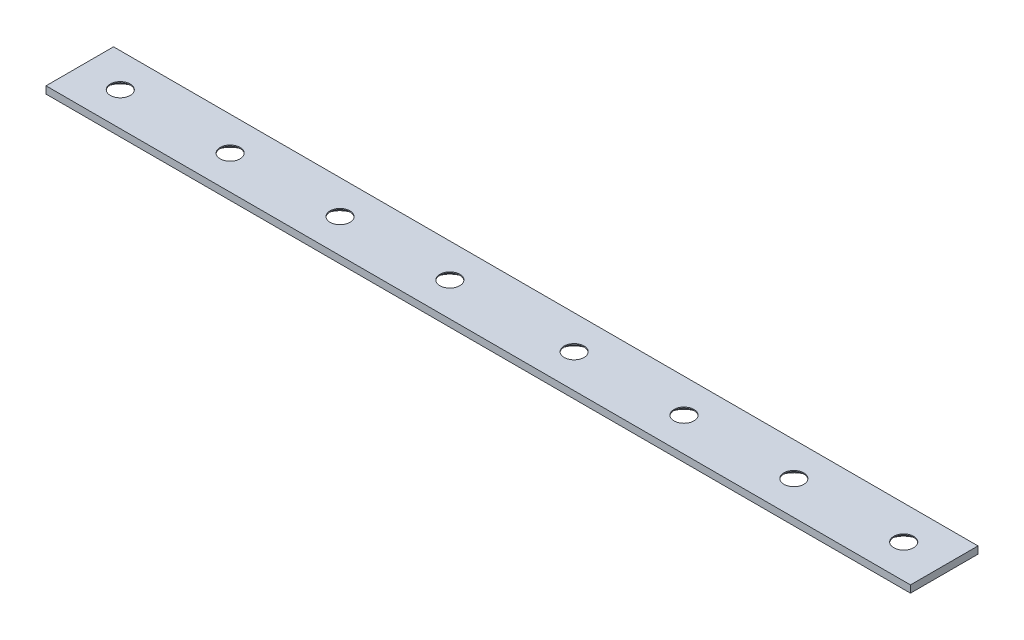
SolidWorks part; units mm, degrees
material "AISI 304"
ref_plane "Front Plane" through (0, 0, 0) normal (0, 0, 1) x (1, 0, 0)
ref_plane "Top Plane" through (0, 0, 0) normal (0, 1, 0) x (1, 0, 0)
ref_plane "Right Plane" through (0, 0, 0) normal (1, 0, 0) x (0, 0, -1)
sketch "Sketch1" plane through (0, 0, 0) normal (0, 1, 0) x (1, 0, 0)
  line L1 (0, 0) -> (243.84, 0)
  line L2 (0, 0) -> (0, 19.05)
  line L3 (0, 19.05) -> (243.84, 19.05)
  line L4 (243.84, 0) -> (243.84, 19.05)
  line L5 (121.92, 19.05) -> (121.92, 0) construction
  line L6 (0, 9.525) -> (243.84, 9.525) construction
  point P4 (139.446, 9.525)
  point P5 (170.434, 9.525)
  point P6 (201.422, 9.525)
  point P7 (232.41, 9.525)
  point P8 (11.43, 9.525)
  point P9 (42.418, 9.525)
  point P10 (73.406, 9.525)
  point P11 (104.394, 9.525)
  point P192 (121.92, 9.525)
  dimension "D1" = 243.84
  dimension "D2" = 19.05
  dimension "D3" = 30.988
  dimension "D4" = 35.052
  dimension "D5" = 30.988
  dimension "D6" = 30.988
extrude "Boss-Extrude1" add sketch "Sketch1" along normal blind 2.032 contours L3 L4 L1 L2
hole_wizard "CSK for #10 Flat Head Machine Screw (100)1" positions "Sketch2" profile "Sketch3" countersink size "#10" standard "ANSI Inch" end condition through all
sketch "Sketch2" plane through (0, 0, 0) normal (0, -1, 0) x (-1, 0, 0)
  point P0 (-11.43, 9.525)
  point P3 (-42.418, 9.525)
  point P6 (-73.406, 9.525)
  point P9 (-104.394, 9.525)
  point P12 (-139.446, 9.525)
  point P15 (-170.434, 9.525)
  point P18 (-201.422, 9.525)
  point P21 (-232.41, 9.525)
sketch "Sketch3" plane through (11.43, 0, -9.525) normal (1, 0, 0) x (0, 0, -1)
  line L0 (0, 0) -> (0, 2.032)
  line L1 (0, 2.032) -> (2.8067, 2.032)
  line L2 (2.8067, 2.032) -> (2.8067, 1.7477)
  line L3 (2.8067, 1.7477) -> (4.8895, 0)
  line L5 (4.8895, 0) -> (0, 0)
  line L6 (-2.8067, 1.7477) -> (-4.8895, 0) construction
  line L11 (0, -6.35) -> (0, 107.95) construction
  dimension "Thru Hole Dia." = 5.6134
  dimension "Thru Hole Depth" = 2.032
  dimension "Near C'Sink Dia." = 9.779
  dimension "Near C'Sink Angle" = 100
ref_plane "Plane1" through (201.422, 0, 0) normal (1, 0, 0) x (0, 0, -1)
ref_plane "Plane2" through (232.41, 0, 0) normal (1, 0, 0) x (0, 0, -1)
